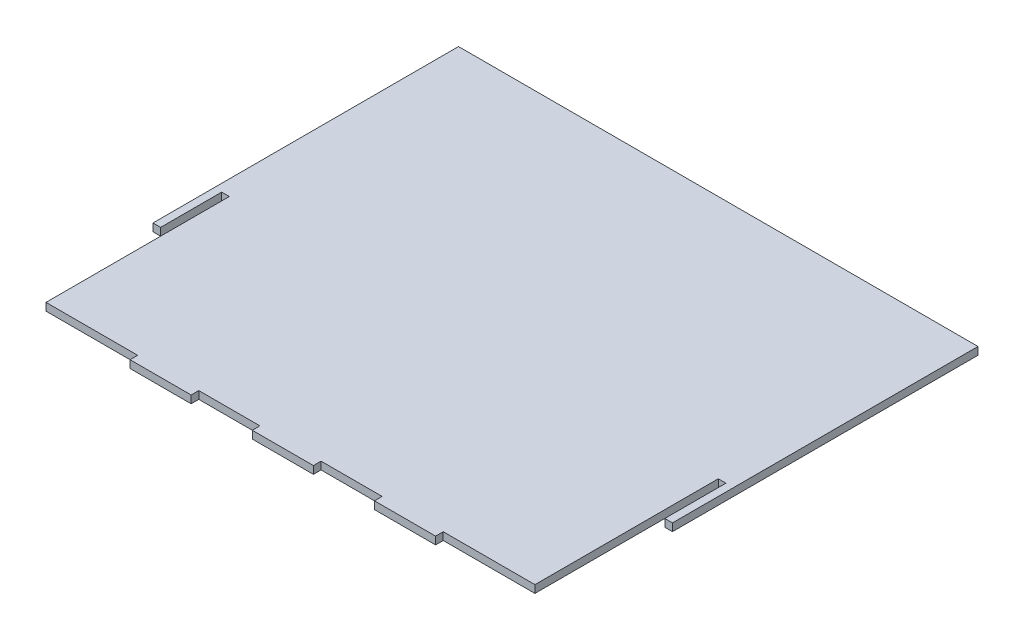
SolidWorks part; units mm, degrees
ref_plane "Front Plane" through (0, 0, 0) normal (0, 0, 1) x (1, 0, 0)
ref_plane "Top Plane" through (0, 0, 0) normal (0, 1, 0) x (1, 0, 0)
ref_plane "Right Plane" through (0, 0, 0) normal (1, 0, 0) x (0, 0, -1)
sketch "Sketch1" plane through (0, 0, 0) normal (0, 1, 0) x (1, 0, 0)
  line L0 (-38.1, -92.075) -> (-12.7, -92.075) construction
  line L1 (-107.95, -88.9) -> (107.95, -88.9)
  line L2 (-107.95, -88.9) -> (-107.95, 88.9)
  line L3 (-107.95, 88.9) -> (107.95, 88.9)
  line L4 (107.95, -88.9) -> (107.95, 88.9)
  line L5 (-107.95, -88.9) -> (107.95, 88.9) construction
  line L6 (-107.95, 88.9) -> (107.95, -88.9) construction
  line L7 (-12.7, -88.9) -> (12.7, -88.9)
  line L8 (-12.7, -88.9) -> (-12.7, -92.075)
  line L9 (-12.7, -92.075) -> (12.7, -92.075)
  line L10 (12.7, -88.9) -> (12.7, -92.075)
  line L11 (38.1, -88.9) -> (63.5, -88.9)
  line L12 (38.1, -88.9) -> (38.1, -92.075)
  line L13 (38.1, -92.075) -> (63.5, -92.075)
  line L14 (63.5, -88.9) -> (63.5, -92.075)
  line L15 (-63.5, -88.9) -> (-38.1, -88.9)
  line L16 (-63.5, -88.9) -> (-63.5, -92.075)
  line L17 (-63.5, -92.075) -> (-38.1, -92.075)
  line L18 (-38.1, -88.9) -> (-38.1, -92.075)
  line L19 (12.7, -92.075) -> (38.1, -92.075) construction
  line L20 (101.6, -88.9) -> (101.6, -12.7)
  line L21 (101.6, -12.7) -> (104.775, -12.7)
  line L22 (104.775, -12.7) -> (104.775, -38.1)
  line L23 (104.775, -38.1) -> (107.95, -38.1)
  line L24 (-101.6, -88.9) -> (-101.6, -12.7)
  line L25 (-101.6, -12.7) -> (-104.775, -12.7)
  line L26 (-104.775, -12.7) -> (-104.775, -38.1)
  line L27 (-104.775, -38.1) -> (-107.95, -38.1)
  point P0 (0, 0)
  point P18 (0, -92.075)
  point P26 (102.238, -30.661)
  dimension "D1" = 215.9
  dimension "D2" = 177.8
  dimension "D3" = 25.4
  dimension "D4" = 3.175
  dimension "D5" = 3.175
  dimension "D6" = 76.2
  dimension "D7" = 25.4
extrude "Boss-Extrude1" add sketch "Sketch1" along normal mid plane 3.175
